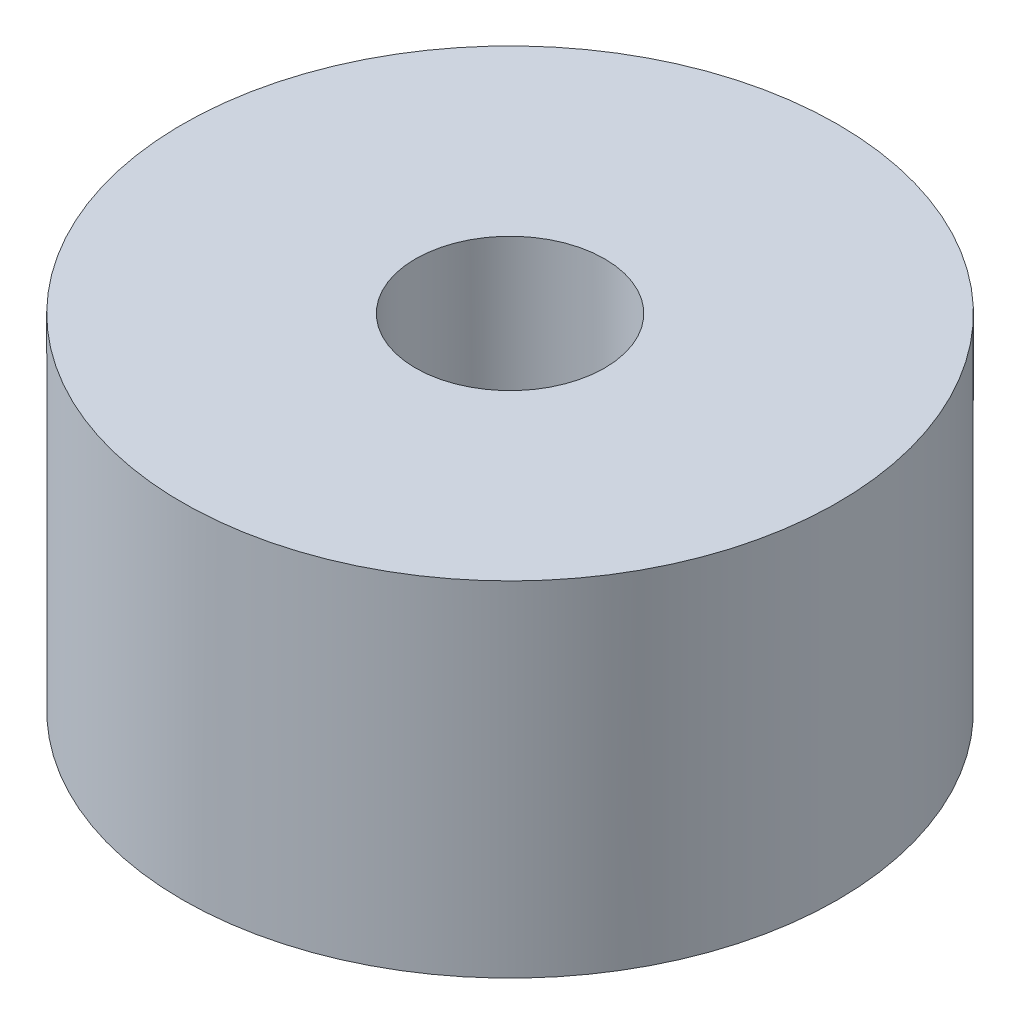
SolidWorks part; units mm, degrees
material "Nylon 101"
ref_plane "Front Plane" through (0, 0, 0) normal (0, 0, 1) x (1, 0, 0)
ref_plane "Top Plane" through (0, 0, 0) normal (0, 1, 0) x (1, 0, 0)
ref_plane "Right Plane" through (0, 0, 0) normal (1, 0, 0) x (0, 0, -1)
sketch "Sketch2" plane through (0, 0, 0) normal (0, 1, 0) x (1, 0, 0)
  circle A0 centre (0, 0) radius 9.525
  dimension "D1" = 19.05
extrude "Boss-Extrude1" add sketch "Sketch2" along normal blind 1
sketch "Sketch4" plane through (0, 1, 0) normal (0, 1, 0) x (1, 0, 0)
  point P0 (0, 0)
hole_wizard "M5 Clearance Hole1" positions "Sketch5" profile "Sketch6" hole size "M5" standard "AS" end condition through all
sketch "Sketch5" plane through (0, 1, 0) normal (0, 1, 0) x (1, 0, 0)
  point P0 (0, 0)
sketch "Sketch6" plane through (0, 1, 0) normal (1, 0, 0) x (0, 0, 1)
  line L0 (0, 0) -> (0, 1)
  line L1 (0, 1) -> (2.75, 1)
  line L2 (2.75, 1) -> (2.75, 0)
  line L5 (2.75, 0) -> (0, 0)
  line L11 (0, -6.35) -> (0, 107.95) construction
  dimension "Thru Hole Dia." = 5.5
  dimension "Thru Hole Depth" = 1
sketch "Sketch7" plane through (0, 1, 0) normal (0, 1, 0) x (1, 0, 0)
  line L0 (10.2467, 50.5598) -> (-15.1231, 49.3212) construction
  line L1 (3.0638, 9.0188) -> (-3.9278, 8.6774)
  line L2 (3.0638, 9.0188) -> (3.0314, 9.6843)
  line L3 (3.0314, 9.6843) -> (-3.9603, 9.343)
  line L4 (-3.9278, 8.6774) -> (-3.9603, 9.343)
  circle A0 centre (0, 0) radius 9.525 construction
  dimension "D1" = 7
sketch "Sketch9" plane through (0, 0, 0) normal (0, -1, 0) x (1, 0, 0)
  circle A0 centre (0, 0) radius 9.525
  circle A1 centre (0, 0) radius 2.75
  circle A2 centre (0, 0) radius 9.525 construction
  circle A3 centre (0, 0) radius 2.75 construction
extrude "Cut-Extrude1" cut sketch "Sketch7" against normal through all both and the other way through all
extrude "Boss-Extrude2" add sketch "Sketch9" against normal blind 10
equation "\"keelOutDiameter\"= 1in"
equation "\"keelInDiameter\"= \"keelOutDiameter\" - 0.125in"
equation "\"frontBoltClearance\"= 7.25mm"
equation "\"betweenBoltsDistance\"= 20mm"
equation "\"wingLength\"= 1.4m"
equation "\"frontTubeLength\"= \"wingLength\" / sin ( 34.95deg )"
equation "\"plateThickness\"= 5mm"
equation "\"crossBarOutDiameter\"= 1in"
equation "\"crossBarInDiameter\"= \"crossBarOutDiameter\" - 0.125in"
equation "\"frontToCrossBar\"= 466mm"
equation "\"cablePinDiameter\"= 5mm"
equation "\"D1@Sketch2\"=\"keelOutDiameter\"*0.75"
